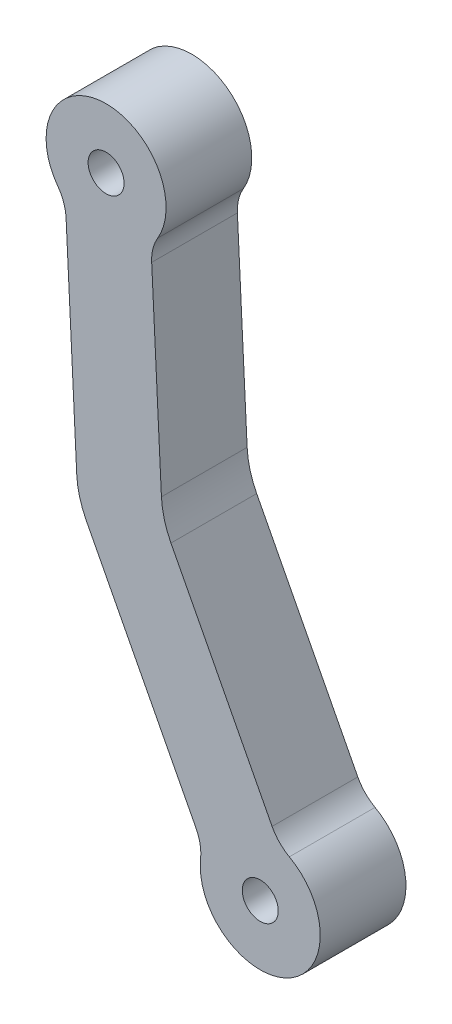
SolidWorks part; units mm, degrees
ref_plane "Alzado" through (0, 0, 0) normal (0, 0, 1) x (1, 0, 0)
ref_plane "Planta" through (0, 0, 0) normal (0, 1, 0) x (1, 0, 0)
ref_plane "Vista lateral" through (0, 0, 0) normal (1, 0, 0) x (0, 0, -1)
sketch "Croquis1" plane through (0, 0, 0) normal (0, 0, 1) x (1, 0, 0)
  line L4 (-43.6853, -9.5091) -> (-55.4849, 13.2227)
  line L5 (-65.3657, 10.5523) -> (-52.5608, -14.1162)
  line L6 (-56.5974, 17.3388) -> (-57.7341, 40.4608)
  line L7 (-67.722, 39.9697) -> (-66.4782, 14.6684)
  circle A10 centre (-45.067, -17.7) radius 2.1
  arc A11 (-52.027, -16.9532) -> (-52.5608, -14.1162) centre (-56.9985, -16.4198) ccw
  arc A12 (-52.027, -16.9532) -> (-41.6723, -11.5782) centre (-45.067, -17.7) ccw
  arc A13 (-43.6853, -9.5091) -> (-41.6723, -11.5782) centre (-39.2475, -7.2055) ccw
  arc A14 (-66.4782, 14.6684) -> (-65.3657, 10.5523) centre (-56.4902, 15.1594) ccw
  arc A15 (-56.5974, 17.3388) -> (-55.4849, 13.2227) centre (-46.6095, 17.8298) ccw
  arc A16 (-57.0375, 43.2622) -> (-57.7341, 40.4608) centre (-52.7401, 40.7063) ccw
  arc A17 (-67.722, 39.9697) -> (-68.6901, 42.6893) centre (-72.716, 39.7242) ccw
  circle A18 centre (-63.0538, 46.8405) radius 2.1
  arc A19 (-57.0375, 43.2622) -> (-68.6901, 42.6893) centre (-63.0538, 46.8405) ccw
  point P1 (0, 0)
  point P11 (0, 0)
  point P14 (0, 0)
  dimension "D1" = 4.2
extrude "Saliente-Extruir1" add sketch "Croquis1" along normal blind 10
